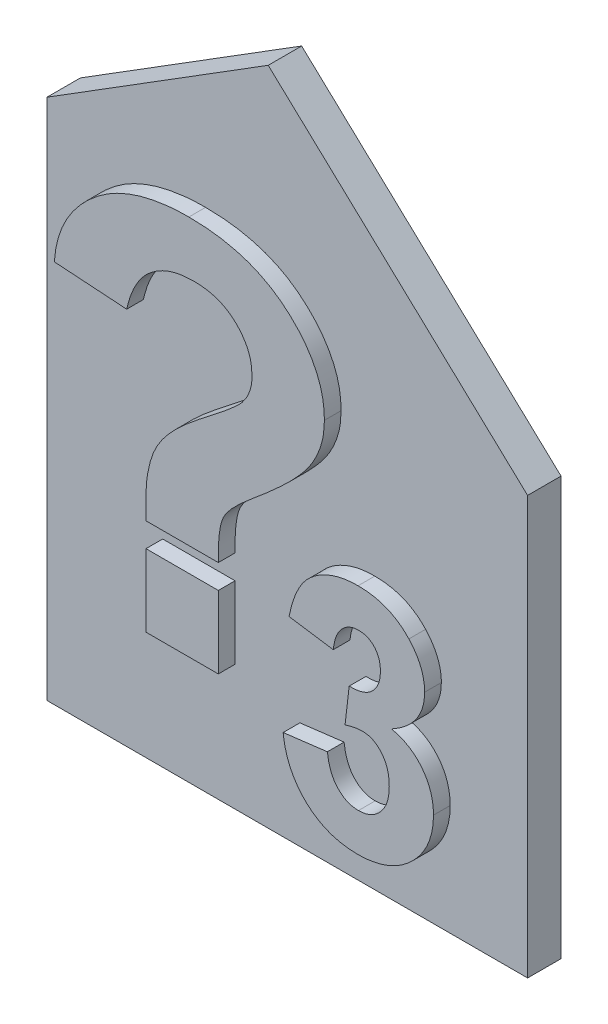
SolidWorks part; units mm, degrees
ref_plane "Přední rovina" through (0, 0, 0) normal (0, 0, 1) x (1, 0, 0)
ref_plane "Horní rovina" through (0, 0, 0) normal (0, 1, 0) x (1, 0, 0)
ref_plane "Pravá rovina" through (0, 0, 0) normal (1, 0, 0) x (0, 0, -1)
sketch "Skica1" plane through (0, 0, 0) normal (0, 0, 1) x (1, 0, 0)
  line L0 (-66.5051, 0) -> (66.5051, 0) construction
  line L1 (0, 0) -> (0, 20)
  line L2 (0, 20) -> (-12.4128, 31.6156)
  line L3 (-12.4128, 31.6156) -> (-23, 25)
  line L4 (-23, 25) -> (-23, 0)
  line L5 (-23, 0) -> (0, 0)
  dimension "D1" = 23
  dimension "D2" = 25
  dimension "D3" = 20
  dimension "D4" = 17
  dimension "D5" = 122
extrude "Přidat vysunutím5" add sketch "Skica1" along normal blind 1.6
sketch "Skica2" plane through (0, 0, 1.6) normal (0, 0, 1) x (1, 0, 0)
  line L0 (-23, 6) -> (0, 6) construction
  line L1 (-23, 25) -> (-23, 0) construction
  line L2 (0, 0) -> (0, 20) construction
  line L3 (-3, 0) -> (-3, 22.8073) construction
  line L4 (-23, 0) -> (0, 0) construction
  line L5 (0, 20) -> (-12.4128, 31.6156) construction
  line L6 (-23, 2) -> (-3, 2) construction
  text T0 "?" font "Arial" height 18
  text T1 "3" font "Arial" height 11
  dimension "D1" = 6
  dimension "D2" = 3
  dimension "D3" = 2
extrude "Přidat vysunutím7" add sketch "Skica2" along normal blind 0.8
